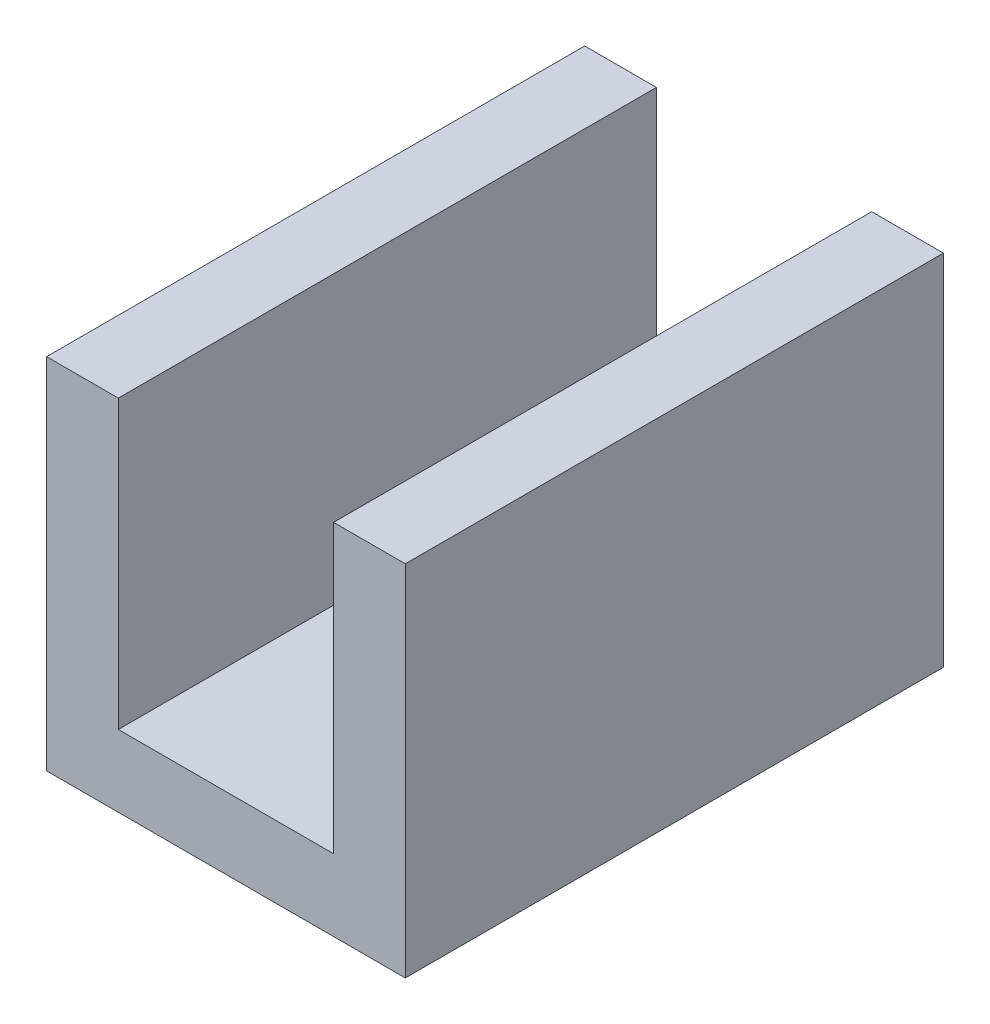
SolidWorks part; units mm, degrees
ref_plane "Front Plane" through (0, 0, 0) normal (0, 0, 1) x (1, 0, 0)
ref_plane "Top Plane" through (0, 0, 0) normal (0, 1, 0) x (1, 0, 0)
ref_plane "Right Plane" through (0, 0, 0) normal (1, 0, 0) x (0, 0, -1)
sketch "Sketch1" plane through (0, 0, 0) normal (0, 0, 1) x (1, 0, 0)
  line L0 (0, 0) -> (0, 254)
  line L1 (0, 254) -> (50.8, 254)
  line L2 (50.8, 254) -> (50.8, 50.8)
  line L3 (50.8, 50.8) -> (203.2, 50.8)
  line L4 (203.2, 50.8) -> (203.2, 254)
  line L5 (203.2, 254) -> (254, 254)
  line L6 (254, 254) -> (254, 0)
  line L7 (254, 0) -> (0, 0)
  dimension "D1" = 254
  dimension "D2" = 254
  dimension "D3" = 50.8
  dimension "D4" = 50.8
extrude "Boss-Extrude1" add sketch "Sketch1" against normal blind 381
